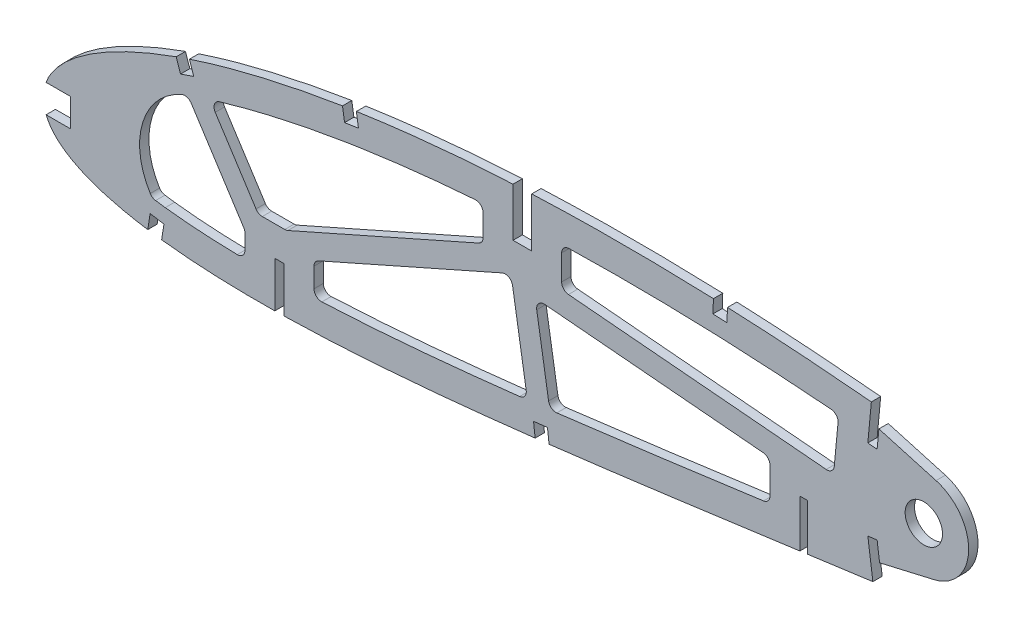
SolidWorks part; units mm, degrees
ref_plane "Front Plane" through (0, 0, 0) normal (0, 0, 1) x (1, 0, 0)
ref_plane "Top Plane" through (0, 0, 0) normal (0, 1, 0) x (1, 0, 0)
ref_plane "Right Plane" through (0, 0, 0) normal (1, 0, 0) x (0, 0, -1)
curve "Curve1"
  spline degree 3 poles (452.1031, 0.7048, 0) (452.0685, 0.7262, 0) (451.9301, 0.8117, 0) (451.6183, 1.003, 0) (451.099, 1.3216, 0) (450.372, 1.7653, 0) (449.438, 2.3329, 0) (448.2963, 3.0204, 0) (446.9478, 3.8257, 0) (445.3928, 4.7448, 0) (443.6314, 5.7736, 0) (441.6643, 6.9077, 0) (439.4916, 8.1409, 0) (437.1143, 9.468, 0) (434.5331, 10.8828, 0) (431.7485, 12.3789, 0) (428.7615, 13.9486, 0) (425.5733, 15.5853, 0) (422.1844, 17.2798, 0) (418.5964, 19.0251, 0) (414.8106, 20.8125, 0) (410.8282, 22.6325, 0) (406.6515, 24.4776, 0) (402.2816, 26.3365, 0) (397.7212, 28.201, 0) (392.972, 30.0605, 0) (388.0369, 31.9065, 0) (382.9178, 33.7272, 0) (377.6186, 35.5144, 0) (372.1418, 37.2567, 0) (366.4913, 38.9446, 0) (360.6704, 40.5671, 0) (354.684, 42.1159, 0) (348.5359, 43.5797, 0) (342.2312, 44.9487, 0) (335.775, 46.2147, 0) (329.1727, 47.3651, 0) (322.4425, 48.3989, 0) (315.6929, 49.2588, 0) (308.9571, 50.1023, 0) (302.2314, 50.8946, 0) (295.4235, 51.6533, 0) (288.5399, 52.3742, 0) (281.5875, 53.055, 0) (274.5733, 53.6928, 0) (267.5046, 54.2857, 0) (260.3883, 54.8303, 0) (253.2318, 55.3259, 0) (246.0422, 55.768, 0) (238.8272, 56.1563, 0) (231.5941, 56.4881, 0) (224.3504, 56.7611, 0) (217.1039, 56.9737, 0) (209.862, 57.1238, 0) (202.6326, 57.2105, 0) (195.4232, 57.2315, 0) (188.2416, 57.1863, 0) (181.0954, 57.0734, 0) (173.9924, 56.8912, 0) (166.9401, 56.6395, 0) (159.9462, 56.3182, 0) (153.0184, 55.9248, 0) (146.164, 55.4618, 0) (139.3909, 54.9271, 0) (132.7063, 54.3206, 0) (126.1174, 53.645, 0) (119.6314, 52.8983, 0) (113.2554, 52.0826, 0) (106.9962, 51.1996, 0) (100.8609, 50.2488, 0) (94.8561, 49.2329, 0) (88.9882, 48.153, 0) (83.2635, 47.0122, 0) (77.6882, 45.8109, 0) (72.2682, 44.5525, 0) (67.0092, 43.2395, 0) (61.9167, 41.874, 0) (56.9959, 40.4594, 0) (52.2519, 38.999, 0) (47.6902, 37.4943, 0) (43.3141, 35.951, 0) (39.1291, 34.3702, 0) (35.1384, 32.7568, 0) (31.3466, 31.113, 0) (27.7567, 29.4439, 0) (24.3726, 27.7512, 0) (21.1967, 26.0397, 0) (18.2324, 24.3122, 0) (15.4823, 22.5717, 0) (12.9477, 20.8227, 0) (10.632, 19.0664, 0) (8.5361, 17.307, 0) (6.6613, 15.5474, 0) (5.0102, 13.7886, 0) (3.5829, 12.0339, 0) (2.3811, 10.2847, 0) (1.4051, 8.5424, 0) (0.6571, 6.8085, 0) (0.1363, 5.084, 0) (-0.1488, 3.3712, 0) (-0.2197, 1.669, 0) (-0.0731, 0.5555, 0) (0, 0, 0) knots 0 0 0 0 0.000254 0.001015 0.002283 0.004057 0.006331 0.009105 0.012374 0.016134 0.02038 0.025106 0.030306 0.035972 0.0421 0.048678 0.055702 0.06316 0.071046 0.07935 0.088063 0.097176 0.106678 0.116562 0.126814 0.137428 0.148394 0.1597 0.171338 0.183298 0.19557 0.208144 0.221012 0.234162 0.247587 0.261277 0.275223 0.289414 0.303771 0.317689 0.331784 0.34604 0.360444 0.374983 0.38964 0.404403 0.419257 0.434187 0.449177 0.464215 0.479284 0.49437 0.509458 0.524532 0.539579 0.554583 0.56953 0.584403 0.599191 0.613877 0.628447 0.642889 0.657186 0.671326 0.685294 0.699078 0.712665 0.726043 0.739198 0.752118 0.764792 0.777208 0.789356 0.801224 0.812804 0.824083 0.835055 0.84571 0.856038 0.866034 0.875689 0.884998 0.893953 0.902553 0.910789 0.918661 0.926166 0.933303 0.940071 0.946475 0.952518 0.958205 0.963547 0.968557 0.97325 0.977651 0.981787 0.985694 0.989415 0.993001 0.996508 1 1 1 1
curve "Curve2"
  spline degree 3 poles (0, 0, 0) (0.1161, -0.5481, 0) (0.3488, -1.6467, 0) (0.9811, -3.2283, 0) (1.8173, -4.7487, 0) (2.8749, -6.2038, 0) (4.147, -7.5932, 0) (5.6306, -8.9184, 0) (7.3243, -10.1787, 0) (9.226, -11.3735, 0) (11.3328, -12.5041, 0) (13.6425, -13.5697, 0) (16.1528, -14.5701, 0) (18.8611, -15.5039, 0) (21.764, -16.3724, 0) (24.8588, -17.1737, 0) (28.1419, -17.9088, 0) (31.6103, -18.5759, 0) (35.26, -19.1755, 0) (39.0874, -19.7075, 0) (43.0885, -20.172, 0) (47.2594, -20.5682, 0) (51.596, -20.8969, 0) (56.0938, -21.1583, 0) (60.7487, -21.3533, 0) (65.556, -21.481, 0) (70.5112, -21.5436, 0) (75.6096, -21.5419, 0) (80.8464, -21.4754, 0) (86.2171, -21.3479, 0) (91.7164, -21.1586, 0) (97.3395, -20.9096, 0) (103.0813, -20.6036, 0) (108.9365, -20.2416, 0) (114.9002, -19.8251, 0) (120.967, -19.3576, 0) (127.1315, -18.8401, 0) (133.3883, -18.2757, 0) (139.7319, -17.6673, 0) (146.1567, -17.0167, 0) (152.6572, -16.327, 0) (159.2275, -15.6004, 0) (165.862, -14.8409, 0) (172.5546, -14.0497, 0) (179.2998, -13.2315, 0) (186.0911, -12.3877, 0) (192.923, -11.5217, 0) (199.7891, -10.6375, 0) (206.6832, -9.7349, 0) (213.5994, -8.8205, 0) (220.5311, -7.8935, 0) (227.4721, -6.9586, 0) (234.4161, -6.0188, 0) (241.3564, -5.0743, 0) (248.2868, -4.1291, 0) (255.2009, -3.1857, 0) (262.0918, -2.2442, 0) (268.9535, -1.3094, 0) (275.779, -0.3811, 0) (282.5619, 0.5389, 0) (289.2958, 1.4477, 0) (295.9744, 2.3443, 0) (302.5907, 3.228, 0) (309.138, 4.0992, 0) (315.5119, 4.9314, 0) (321.6955, 5.769, 0) (327.7099, 6.4556, 0) (333.6493, 7.0417, 0) (339.52, 7.5222, 0) (345.315, 7.9041, 0) (351.0275, 8.19, 0) (356.6509, 8.3839, 0) (362.1779, 8.4917, 0) (367.6017, 8.516, 0) (372.9148, 8.4647, 0) (378.1105, 8.3417, 0) (383.1813, 8.1528, 0) (388.1203, 7.9042, 0) (392.9205, 7.6027, 0) (397.5745, 7.2527, 0) (402.076, 6.8625, 0) (406.4179, 6.4377, 0) (410.5937, 5.9833, 0) (414.5972, 5.5086, 0) (418.4221, 5.0169, 0) (422.0625, 4.5163, 0) (425.5126, 4.0117, 0) (428.7669, 3.5097, 0) (431.8204, 3.015, 0) (434.6681, 2.5342, 0) (437.3055, 2.0718, 0) (439.7281, 1.6323, 0) (441.9324, 1.2212, 0) (443.9143, 0.8406, 0) (445.6709, 0.4968, 0) (447.199, 0.1913, 0) (448.4964, -0.0716, 0) (449.5609, -0.2909, 0) (450.3908, -0.463, 0) (450.9844, -0.5881, 0) (451.3411, -0.6626, 0) (451.4997, -0.6964, 0) (451.5393, -0.7048, 0) knots 0 0 0 0 0.003638 0.007293 0.011028 0.014901 0.018963 0.023258 0.027821 0.032679 0.037853 0.043362 0.049215 0.055422 0.061989 0.068918 0.076211 0.083868 0.091887 0.100266 0.109 0.118085 0.127515 0.137285 0.147388 0.157816 0.168563 0.179619 0.190977 0.202627 0.21456 0.226767 0.239236 0.251959 0.264924 0.27812 0.291536 0.30516 0.318981 0.332985 0.347163 0.361499 0.375981 0.390597 0.405333 0.420175 0.43511 0.450124 0.465203 0.480333 0.495501 0.51069 0.525887 0.541078 0.556247 0.571382 0.586466 0.601485 0.616424 0.631269 0.646007 0.660621 0.675098 0.689423 0.703582 0.716908 0.730009 0.742952 0.755726 0.76832 0.780724 0.792927 0.804916 0.816679 0.828204 0.839475 0.850481 0.861208 0.871639 0.881763 0.891564 0.901027 0.910139 0.918884 0.927249 0.935221 0.942785 0.949928 0.956638 0.962904 0.968712 0.974054 0.978918 0.983297 0.98718 0.990561 0.993433 0.995791 0.99763 0.998946 0.999737 1 1 1 1
sketch "Sketch1" plane through (0, 0, 0) normal (0, 0, 1) x (1, 0, 0)
  line L24 (452.1031, 0.7048) -> (456.094, -1.6764)
  line L25 (451.5393, -0.7048) -> (456.094, -1.6764)
  spline S2 degree 3 poles (-2902.3793, -755.52) (63.6454, 63.6466) (-7.9338, 19.0709) (0.9811, -3.2283) (1.8173, -4.7487) (2.8749, -6.2038) (4.147, -7.5932) (5.6306, -8.9184) (7.3243, -10.1787) (9.226, -11.3735) (11.3328, -12.5041) (13.6425, -13.5697) (16.1528, -14.5701) (18.8611, -15.5039) (21.764, -16.3724) (24.8588, -17.1737) (28.1419, -17.9088) (31.6103, -18.5759) (35.26, -19.1755) (39.0874, -19.7075) (43.0885, -20.172) (47.2594, -20.5682) (51.596, -20.8969) (56.0938, -21.1583) (60.7487, -21.3533) (65.556, -21.481) (70.5112, -21.5436) (75.6096, -21.5419) (80.8464, -21.4754) (86.2171, -21.3479) (91.7164, -21.1586) (97.3395, -20.9096) (103.0813, -20.6036) (108.9365, -20.2416) (114.9002, -19.8251) (120.967, -19.3576) (127.1315, -18.8401) (133.3883, -18.2757) (139.7319, -17.6673) (146.1567, -17.0167) (152.6572, -16.327) (159.2275, -15.6004) (165.862, -14.8409) (172.5546, -14.0497) (179.2998, -13.2315) (186.0911, -12.3877) (192.923, -11.5217) (199.7891, -10.6375) (206.6832, -9.7349) (213.5994, -8.8205) (220.5311, -7.8935) (227.4721, -6.9586) (234.4161, -6.0188) (241.3564, -5.0743) (248.2868, -4.1291) (255.2009, -3.1857) (262.0918, -2.2442) (268.9535, -1.3094) (275.779, -0.3811) (282.5619, 0.5389) (289.2958, 1.4477) (295.9744, 2.3443) (302.5907, 3.228) (309.138, 4.0992) (315.5119, 4.9314) (321.6955, 5.769) (327.7099, 6.4556) (333.6493, 7.0417) (339.52, 7.5222) (345.315, 7.9041) (351.0275, 8.19) (356.6509, 8.3839) (362.1779, 8.4917) (367.6017, 8.516) (372.9148, 8.4647) (378.1105, 8.3417) (383.1813, 8.1528) (388.1203, 7.9042) (392.9205, 7.6027) (397.5745, 7.2527) (402.076, 6.8625) (406.4179, 6.4377) (410.5937, 5.9833) (414.5972, 5.5086) (418.4221, 5.0169) (422.0625, 4.5163) (425.5126, 4.0117) (428.7669, 3.5097) (431.8204, 3.015) (434.6681, 2.5342) (437.3055, 2.0718) (439.7281, 1.6323) (441.9324, 1.2212) (443.9143, 0.8406) (445.6709, 0.4968) (447.199, 0.1913) (448.4964, -0.0716) (449.5609, -0.2909) (450.3908, -0.463) (450.9844, -0.5881) (467.4773, -4.0305) (482.2176, -14.7818) (1120.3699, 2922.8002) knots -0.14446 -0.14446 -0.14446 -0.14446 0.003638 0.007293 0.011028 0.014901 0.018963 0.023258 0.027821 0.032679 0.037853 0.043362 0.049215 0.055422 0.061989 0.068918 0.076211 0.083868 0.091887 0.100266 0.109 0.118085 0.127515 0.137285 0.147388 0.157816 0.168563 0.179619 0.190977 0.202627 0.21456 0.226767 0.239236 0.251959 0.264924 0.27812 0.291536 0.30516 0.318981 0.332985 0.347163 0.361499 0.375981 0.390597 0.405333 0.420175 0.43511 0.450124 0.465203 0.480333 0.495501 0.51069 0.525887 0.541078 0.556247 0.571382 0.586466 0.601485 0.616424 0.631269 0.646007 0.660621 0.675098 0.689423 0.703582 0.716908 0.730009 0.742952 0.755726 0.76832 0.780724 0.792927 0.804916 0.816679 0.828204 0.839475 0.850481 0.861208 0.871639 0.881763 0.891564 0.901027 0.910139 0.918884 0.927249 0.935221 0.942785 0.949928 0.956638 0.962904 0.968712 0.974054 0.978918 0.983297 0.98718 0.990561 0.993433 0.995791 0.99763 0.998946 0.999737 1.107215 1.107215 1.107215 1.107215 only from (0, 0) to (451.5393, -0.7048) construction
  spline S3 degree 3 poles (2072.0463, 2524.7843) (479.969, -24.2918) (467.6474, -8.829) (451.6183, 1.003) (451.099, 1.3216) (450.372, 1.7653) (449.438, 2.3329) (448.2963, 3.0204) (446.9478, 3.8257) (445.3928, 4.7448) (443.6314, 5.7736) (441.6643, 6.9077) (439.4916, 8.1409) (437.1143, 9.468) (434.5331, 10.8828) (431.7485, 12.3789) (428.7615, 13.9486) (425.5733, 15.5853) (422.1844, 17.2798) (418.5964, 19.0251) (414.8106, 20.8125) (410.8282, 22.6325) (406.6515, 24.4776) (402.2816, 26.3365) (397.7212, 28.201) (392.972, 30.0605) (388.0369, 31.9065) (382.9178, 33.7272) (377.6186, 35.5144) (372.1418, 37.2567) (366.4913, 38.9446) (360.6704, 40.5671) (354.684, 42.1159) (348.5359, 43.5797) (342.2312, 44.9487) (335.775, 46.2147) (329.1727, 47.3651) (322.4425, 48.3989) (315.6929, 49.2588) (308.9571, 50.1023) (302.2314, 50.8946) (295.4235, 51.6533) (288.5399, 52.3742) (281.5875, 53.055) (274.5733, 53.6928) (267.5046, 54.2857) (260.3883, 54.8303) (253.2318, 55.3259) (246.0422, 55.768) (238.8272, 56.1563) (231.5941, 56.4881) (224.3504, 56.7611) (217.1039, 56.9737) (209.862, 57.1238) (202.6326, 57.2105) (195.4232, 57.2315) (188.2416, 57.1863) (181.0954, 57.0734) (173.9924, 56.8912) (166.9401, 56.6395) (159.9462, 56.3182) (153.0184, 55.9248) (146.164, 55.4618) (139.3909, 54.9271) (132.7063, 54.3206) (126.1174, 53.645) (119.6314, 52.8983) (113.2554, 52.0826) (106.9962, 51.1996) (100.8609, 50.2488) (94.8561, 49.2329) (88.9882, 48.153) (83.2635, 47.0122) (77.6882, 45.8109) (72.2682, 44.5525) (67.0092, 43.2395) (61.9167, 41.874) (56.9959, 40.4594) (52.2519, 38.999) (47.6902, 37.4943) (43.3141, 35.951) (39.1291, 34.3702) (35.1384, 32.7568) (31.3466, 31.113) (27.7567, 29.4439) (24.3726, 27.7512) (21.1967, 26.0397) (18.2324, 24.3122) (15.4823, 22.5717) (12.9477, 20.8227) (10.632, 19.0664) (8.5361, 17.307) (6.6613, 15.5474) (5.0102, 13.7886) (3.5829, 12.0339) (2.3811, 10.2847) (1.4051, 8.5424) (0.6571, 6.8085) (0.1363, 5.084) (-0.1488, 3.3712) (-1.1473, -20.5831) (81.3582, -38.7525) (-2988.6181, -253.0424) knots -0.115084 -0.115084 -0.115084 -0.115084 0.000254 0.001015 0.002283 0.004057 0.006331 0.009105 0.012374 0.016134 0.02038 0.025106 0.030306 0.035972 0.0421 0.048678 0.055702 0.06316 0.071046 0.07935 0.088063 0.097176 0.106678 0.116562 0.126814 0.137428 0.148394 0.1597 0.171338 0.183298 0.19557 0.208144 0.221012 0.234162 0.247587 0.261277 0.275223 0.289414 0.303771 0.317689 0.331784 0.34604 0.360444 0.374983 0.38964 0.404403 0.419257 0.434187 0.449177 0.464215 0.479284 0.49437 0.509458 0.524532 0.539579 0.554583 0.56953 0.584403 0.599191 0.613877 0.628447 0.642889 0.657186 0.671326 0.685294 0.699078 0.712665 0.726043 0.739198 0.752118 0.764792 0.777208 0.789356 0.801224 0.812804 0.824083 0.835055 0.84571 0.856038 0.866034 0.875689 0.884998 0.893953 0.902553 0.910789 0.918661 0.926166 0.933303 0.940071 0.946475 0.952518 0.958205 0.963547 0.968557 0.97325 0.977651 0.981787 0.985694 0.989415 0.993001 0.996508 1.138367 1.138367 1.138367 1.138367 only from (452.1031, 0.7048) to (0, 0) construction
  spline S4 degree 3 poles (0, 0) (0.1161, -0.5481) (0.3488, -1.6467) (0.9811, -3.2283) (1.8173, -4.7487) (2.8749, -6.2038) (4.147, -7.5932) (5.6306, -8.9184) (7.3243, -10.1787) (9.226, -11.3735) (11.3328, -12.5041) (13.6425, -13.5697) (16.1528, -14.5701) (18.8611, -15.5039) (21.764, -16.3724) (24.8588, -17.1737) (28.1419, -17.9088) (31.6103, -18.5759) (35.26, -19.1755) (39.0874, -19.7075) (43.0885, -20.172) (47.2594, -20.5682) (51.596, -20.8969) (56.0938, -21.1583) (60.7487, -21.3533) (65.556, -21.481) (70.5112, -21.5436) (75.6096, -21.5419) (80.8464, -21.4754) (86.2171, -21.3479) (91.7164, -21.1586) (97.3395, -20.9096) (103.0813, -20.6036) (108.9365, -20.2416) (114.9002, -19.8251) (120.967, -19.3576) (127.1315, -18.8401) (133.3883, -18.2757) (139.7319, -17.6673) (146.1567, -17.0167) (152.6572, -16.327) (159.2275, -15.6004) (165.862, -14.8409) (172.5546, -14.0497) (179.2998, -13.2315) (186.0911, -12.3877) (192.923, -11.5217) (199.7891, -10.6375) (206.6832, -9.7349) (213.5994, -8.8205) (220.5311, -7.8935) (227.4721, -6.9586) (234.4161, -6.0188) (241.3564, -5.0743) (248.2868, -4.1291) (255.2009, -3.1857) (262.0918, -2.2442) (268.9535, -1.3094) (275.779, -0.3811) (282.5619, 0.5389) (289.2958, 1.4477) (295.9744, 2.3443) (302.5907, 3.228) (309.138, 4.0992) (315.5119, 4.9314) (321.6955, 5.769) (327.7099, 6.4556) (333.6493, 7.0417) (339.52, 7.5222) (345.315, 7.9041) (351.0275, 8.19) (356.6509, 8.3839) (362.1779, 8.4917) (367.6017, 8.516) (372.9148, 8.4647) (378.1105, 8.3417) (383.1813, 8.1528) (388.1203, 7.9042) (392.9205, 7.6027) (397.5745, 7.2527) (402.076, 6.8625) (406.4179, 6.4377) (410.5937, 5.9833) (414.5972, 5.5086) (418.4221, 5.0169) (422.0625, 4.5163) (425.5126, 4.0117) (428.7669, 3.5097) (431.8204, 3.015) (434.6681, 2.5342) (437.3055, 2.0718) (439.7281, 1.6323) (441.9324, 1.2212) (443.9143, 0.8406) (445.6709, 0.4968) (447.199, 0.1913) (448.4964, -0.0716) (449.5609, -0.2909) (450.3908, -0.463) (450.9844, -0.5881) (451.3411, -0.6626) (451.4997, -0.6964) (451.5393, -0.7048) knots 0 0 0 0 0.003638 0.007293 0.011028 0.014901 0.018963 0.023258 0.027821 0.032679 0.037853 0.043362 0.049215 0.055422 0.061989 0.068918 0.076211 0.083868 0.091887 0.100266 0.109 0.118085 0.127515 0.137285 0.147388 0.157816 0.168563 0.179619 0.190977 0.202627 0.21456 0.226767 0.239236 0.251959 0.264924 0.27812 0.291536 0.30516 0.318981 0.332985 0.347163 0.361499 0.375981 0.390597 0.405333 0.420175 0.43511 0.450124 0.465203 0.480333 0.495501 0.51069 0.525887 0.541078 0.556247 0.571382 0.586466 0.601485 0.616424 0.631269 0.646007 0.660621 0.675098 0.689423 0.703582 0.716908 0.730009 0.742952 0.755726 0.76832 0.780724 0.792927 0.804916 0.816679 0.828204 0.839475 0.850481 0.861208 0.871639 0.881763 0.891564 0.901027 0.910139 0.918884 0.927249 0.935221 0.942785 0.949928 0.956638 0.962904 0.968712 0.974054 0.978918 0.983297 0.98718 0.990561 0.993433 0.995791 0.99763 0.998946 0.999737 1 1 1 1
  spline S5 degree 3 poles (452.1031, 0.7048) (452.0685, 0.7262) (451.9301, 0.8117) (451.6183, 1.003) (451.099, 1.3216) (450.372, 1.7653) (449.438, 2.3329) (448.2963, 3.0204) (446.9478, 3.8257) (445.3928, 4.7448) (443.6314, 5.7736) (441.6643, 6.9077) (439.4916, 8.1409) (437.1143, 9.468) (434.5331, 10.8828) (431.7485, 12.3789) (428.7615, 13.9486) (425.5733, 15.5853) (422.1844, 17.2798) (418.5964, 19.0251) (414.8106, 20.8125) (410.8282, 22.6325) (406.6515, 24.4776) (402.2816, 26.3365) (397.7212, 28.201) (392.972, 30.0605) (388.0369, 31.9065) (382.9178, 33.7272) (377.6186, 35.5144) (372.1418, 37.2567) (366.4913, 38.9446) (360.6704, 40.5671) (354.684, 42.1159) (348.5359, 43.5797) (342.2312, 44.9487) (335.775, 46.2147) (329.1727, 47.3651) (322.4425, 48.3989) (315.6929, 49.2588) (308.9571, 50.1023) (302.2314, 50.8946) (295.4235, 51.6533) (288.5399, 52.3742) (281.5875, 53.055) (274.5733, 53.6928) (267.5046, 54.2857) (260.3883, 54.8303) (253.2318, 55.3259) (246.0422, 55.768) (238.8272, 56.1563) (231.5941, 56.4881) (224.3504, 56.7611) (217.1039, 56.9737) (209.862, 57.1238) (202.6326, 57.2105) (195.4232, 57.2315) (188.2416, 57.1863) (181.0954, 57.0734) (173.9924, 56.8912) (166.9401, 56.6395) (159.9462, 56.3182) (153.0184, 55.9248) (146.164, 55.4618) (139.3909, 54.9271) (132.7063, 54.3206) (126.1174, 53.645) (119.6314, 52.8983) (113.2554, 52.0826) (106.9962, 51.1996) (100.8609, 50.2488) (94.8561, 49.2329) (88.9882, 48.153) (83.2635, 47.0122) (77.6882, 45.8109) (72.2682, 44.5525) (67.0092, 43.2395) (61.9167, 41.874) (56.9959, 40.4594) (52.2519, 38.999) (47.6902, 37.4943) (43.3141, 35.951) (39.1291, 34.3702) (35.1384, 32.7568) (31.3466, 31.113) (27.7567, 29.4439) (24.3726, 27.7512) (21.1967, 26.0397) (18.2324, 24.3122) (15.4823, 22.5717) (12.9477, 20.8227) (10.632, 19.0664) (8.5361, 17.307) (6.6613, 15.5474) (5.0102, 13.7886) (3.5829, 12.0339) (2.3811, 10.2847) (1.4051, 8.5424) (0.6571, 6.8085) (0.1363, 5.084) (-0.1488, 3.3712) (-0.2197, 1.669) (-0.0731, 0.5555) (0, 0) knots 0 0 0 0 0.000254 0.001015 0.002283 0.004057 0.006331 0.009105 0.012374 0.016134 0.02038 0.025106 0.030306 0.035972 0.0421 0.048678 0.055702 0.06316 0.071046 0.07935 0.088063 0.097176 0.106678 0.116562 0.126814 0.137428 0.148394 0.1597 0.171338 0.183298 0.19557 0.208144 0.221012 0.234162 0.247587 0.261277 0.275223 0.289414 0.303771 0.317689 0.331784 0.34604 0.360444 0.374983 0.38964 0.404403 0.419257 0.434187 0.449177 0.464215 0.479284 0.49437 0.509458 0.524532 0.539579 0.554583 0.56953 0.584403 0.599191 0.613877 0.628447 0.642889 0.657186 0.671326 0.685294 0.699078 0.712665 0.726043 0.739198 0.752118 0.764792 0.777208 0.789356 0.801224 0.812804 0.824083 0.835055 0.84571 0.856038 0.866034 0.875689 0.884998 0.893953 0.902553 0.910789 0.918661 0.926166 0.933303 0.940071 0.946475 0.952518 0.958205 0.963547 0.968557 0.97325 0.977651 0.981787 0.985694 0.989415 0.993001 0.996508 1 1 1 1
extrude "Boss-Extrude1" add sketch "Sketch1" along normal blind 3.175
sketch "Sketch2" plane through (0, 0, 0) normal (0, 0, -1) x (-1, 0, 0)
  line L0 (-81.6491, -6.0107) -> (-78.4741, -6.0107)
  line L1 (-81.6491, -20.9228) -> (-81.6491, -22.4869)
  line L2 (-259.4491, 13.2207) -> (-259.4491, -2.6526)
  line L4 (-81.6491, -22.4869) -> (-78.4741, -21.7048)
  line L5 (-78.4741, -21.7048) -> (-78.4741, -20.9228)
  line L7 (-165.7866, 56.5935) -> (-165.7866, 39.7629)
  line L8 (-165.7866, 39.7629) -> (-159.4366, 39.7629)
  line L9 (-165.7866, 56.5935) -> (-165.7866, 58.5208)
  line L10 (-81.6491, -6.0107) -> (-81.6491, -20.9228)
  line L12 (-165.7866, 58.5208) -> (-159.4366, 57.5572)
  line L13 (-159.4366, 57.5572) -> (-159.4366, 56.5935)
  line L14 (-78.4741, -6.0107) -> (-78.4741, -20.9228)
  line L16 (-259.4491, 13.2207) -> (-256.9091, 13.2207)
  line L17 (-259.4491, -2.6526) -> (-259.4491, -5.0698)
  line L19 (-159.4366, 56.5935) -> (-159.4366, 39.7629)
  line L20 (-259.4491, -5.0698) -> (-256.9091, -3.8612)
  line L21 (-256.9091, -3.8612) -> (-256.9091, -2.6526)
  line L22 (-256.9091, 13.2207) -> (-256.9091, -2.6526)
extrude "Cut-Extrude1" cut sketch "Sketch2" against normal blind 7.62
sketch "Sketch3" plane through (0, 0, 0) normal (0, 0, -1) x (-1, 0, 0)
  circle A1 centre (-299.0384, 26.2554) radius 6.35
extrude "Cut-Extrude2" cut sketch "Sketch3" against normal blind 7.62
sketch "Sketch4" plane through (0, 0, 3.175) normal (0, 0, 1) x (1, 0, 0)
  line L0 (283.1634, 40.1032) -> (284.3809, 52.7385)
  line L1 (283.1634, 40.1032) -> (284.3809, 52.7385)
  line L2 (284.8624, 0.8345) -> (283.1634, 13.4207)
  line L3 (284.8624, 0.8345) -> (283.1634, 13.4207)
  line L4 (283.1634, 13.4207) -> (280.017, 12.9956)
  line L5 (283.1634, 13.4207) -> (280.017, 12.9956)
  line L6 (280.003, 40.404) -> (283.1634, 40.1032)
  line L7 (280.003, 40.404) -> (283.1634, 40.1032)
  line L8 (280.017, 12.9956) -> (281.7174, 0.4099)
  line L9 (280.017, 12.9956) -> (281.7174, 0.4099)
  line L10 (281.2061, 53.046) -> (280.003, 40.404)
  line L11 (281.2061, 53.046) -> (280.003, 40.404)
  line L12 (227.543, 56.7883) -> (227.3611, 52.0373)
  line L13 (227.543, 56.7883) -> (227.3611, 52.0373)
  line L14 (101.4521, 50.4601) -> (102.1913, 45.7722)
  line L15 (101.4521, 50.4601) -> (102.1913, 45.7722)
  line L16 (44.909, 36.6556) -> (46.4387, 32.1792)
  line L17 (44.909, 36.6556) -> (46.4387, 32.1792)
  line L18 (166.4044, -10.0397) -> (166.9563, -14.7725)
  line L19 (166.4044, -10.0397) -> (166.9563, -14.7725)
  line L20 (36.1137, -14.0525) -> (35.373, -18.771)
  line L21 (36.1137, -14.0525) -> (35.373, -18.771)
  line L22 (40.8104, -14.7911) -> (36.1137, -14.0525)
  line L23 (40.8104, -14.7911) -> (36.1137, -14.0525)
  line L24 (171.134, -9.4806) -> (166.4044, -10.0397)
  line L25 (171.134, -9.4806) -> (166.4044, -10.0397)
  line L26 (50.9453, 33.7189) -> (49.4124, 38.2061)
  line L27 (50.9453, 33.7189) -> (49.4124, 38.2061)
  line L28 (40.0562, -19.5592) -> (40.8104, -14.7911)
  line L29 (40.0562, -19.5592) -> (40.8104, -14.7911)
  line L30 (106.9007, 46.4815) -> (106.1899, 51.2009)
  line L31 (106.9007, 46.4815) -> (106.1899, 51.2009)
  line L32 (232.1192, 51.8391) -> (232.3281, 56.5914)
  line L33 (232.1192, 51.8391) -> (232.3281, 56.5914)
  line L34 (171.6935, -14.2138) -> (171.134, -9.4806)
  line L35 (171.6935, -14.2138) -> (171.134, -9.4806)
  line L36 (227.3611, 52.0373) -> (232.1192, 51.8391)
  line L37 (227.3611, 52.0373) -> (232.1192, 51.8391)
  line L38 (102.1913, 45.7722) -> (106.9007, 46.4815)
  line L39 (102.1913, 45.7722) -> (106.9007, 46.4815)
  line L40 (-0.4483, -2.6341) -> (9.0767, -2.6341)
  line L41 (-0.4483, -2.6341) -> (9.0767, -2.6341)
  line L42 (-0.4483, 6.8909) -> (9.0767, 6.8909)
  line L43 (-0.4483, 6.8909) -> (9.0767, 6.8909)
  line L44 (9.0767, -2.6341) -> (9.0767, 6.8909)
  line L45 (9.0767, -2.6341) -> (9.0767, 6.8909)
  line L46 (46.4387, 32.1792) -> (50.9453, 33.7189)
  line L47 (46.4387, 32.1792) -> (50.9453, 33.7189)
  line L48 (281.7174, 0.4099) -> (282.0892, -2.3425)
  line L49 (282.0892, -2.3425) -> (285.2356, -1.9174)
  line L50 (285.2356, -1.9174) -> (284.8624, 0.8345)
  line L51 (281.2061, 53.046) -> (281.5903, 57.0828)
  line L52 (281.5903, 57.0828) -> (284.7703, 56.7802)
  line L53 (284.7703, 56.7802) -> (284.3809, 52.7385)
  line L54 (227.543, 56.7883) -> (232.3281, 56.5914)
  line L55 (101.4521, 50.4601) -> (106.1899, 51.2009)
  line L56 (44.909, 36.6556) -> (49.4124, 38.2061)
  line L57 (-0.4483, -2.6341) -> (-0.4483, 6.8909)
  line L58 (35.373, -18.771) -> (34.8729, -21.9571)
  line L59 (34.8729, -21.9571) -> (39.5676, -22.6941)
  line L60 (39.5676, -22.6941) -> (40.0562, -19.5592)
  line L61 (166.9563, -14.7725) -> (171.6935, -14.2138)
  line L62 (283.7722, 46.4209) -> (303.193, 40.9182)
  line L63 (284.0129, 7.1276) -> (302.4805, 11.4092)
  line L64 (284.3809, 52.7385) -> (466.0882, 52.7385)
  line L65 (466.0882, 52.7385) -> (466.0882, -18.771)
  line L66 (466.0882, -18.771) -> (284.8624, 0.8345)
  circle A0 centre (299.0384, 26.2554) radius 6.35 construction
  circle A1 centre (299.0384, 26.2554) radius 6.35
  circle A2 centre (299.0384, 26.2554) radius 15.24
  dimension "D1" = 30.48
extrude "Cut-Extrude3" cut sketch "Sketch4" against normal through all
sketch "Sketch5" plane through (0, 0, 3.175) normal (0, 0, 1) x (1, 0, 0)
  line L0 (36.8297, -9.1216) -> (41.2489, -9.7235)
  line L1 (48.3594, 26.9518) -> (52.6619, 28.4309)
  line L2 (103.0835, 40.3016) -> (107.7147, 41.0203)
  line L3 (227.1599, 46.4854) -> (231.8893, 46.2967)
  line L4 (165.7688, -4.6187) -> (170.4819, -4.0617)
  line L5 (169.5966, 39.7629) -> (169.5966, 56.2793)
  line L6 (68.3141, -21.5029) -> (68.3141, 4.1493)
  line L7 (68.3141, 4.1493) -> (91.8091, 4.1493)
  line L8 (91.8091, 4.1493) -> (91.8091, -21.4504)
  line L9 (175.9466, 56.5794) -> (175.9466, 29.6029)
  line L10 (175.9466, 29.6029) -> (149.2766, 29.6029)
  line L11 (149.2766, 29.6029) -> (149.2766, 56.2793)
  line L12 (246.7491, -2.9522) -> (246.7491, 23.3807)
  line L13 (246.7491, 23.3807) -> (269.6091, 23.3807)
  line L14 (269.6091, 23.3807) -> (269.6091, -2.6054)
  line L15 (268.177, 23.3807) -> (271.0953, 54.0451)
  line L16 (269.8887, 41.3666) -> (271.0953, 54.0451) construction
  line L17 (52.6619, 28.4309) -> (68.3141, 4.1493) construction
  line L18 (91.8091, 4.1493) -> (149.2766, 29.6029) construction
  line L19 (168.1254, -4.3402) -> (162.6116, 29.6029) construction
  line L20 (246.7491, 23.3807) -> (175.9466, 29.6029) construction
  line L21 (48.9512, 27.1553) -> (68.3141, -2.8828)
  line L22 (91.8091, -0.0177) -> (158.6846, 29.6029)
  line L23 (171.9123, -3.8905) -> (166.3723, 30.2138)
  line L24 (268.3602, 25.3062) -> (175.9466, 33.4276)
  line L25 (55.8642, 30.4952) -> (72.8471, 4.1493)
  line L26 (82.4011, 4.1493) -> (149.2766, 33.7699)
  line L27 (164.3647, -4.9511) -> (158.7516, 29.6029)
  line L28 (246.7491, 19.5561) -> (166.9646, 26.5675)
  line L29 (49.4595, 26.3667) -> (65.1117, 2.085) construction
  line L30 (55.8642, 30.4952) -> (71.5164, 6.2135) construction
  line L31 (90.2661, 7.6329) -> (147.7336, 33.0865) construction
  line L32 (93.352, 0.6657) -> (150.8195, 26.1193) construction
  line L33 (246.4155, 19.5854) -> (175.613, 25.8075) construction
  line L34 (247.0826, 27.1761) -> (176.2801, 33.3982) construction
  line L35 (164.3647, -4.9511) -> (158.8509, 28.992) construction
  line L36 (9.0767, 6.8909) -> (9.0767, -2.6341)
  line L37 (9.0767, -2.6341) -> (0.7554, -2.6341)
  line L38 (35.3108, -19.1674) -> (36.1137, -14.0525)
  line L39 (36.1137, -14.0525) -> (40.8104, -14.7911)
  line L40 (40.8104, -14.7911) -> (40.0562, -19.5592)
  line L41 (40.0562, -19.5592) -> (40.0174, -19.8086)
  line L42 (78.4741, -21.5029) -> (78.4741, -6.0107)
  line L43 (78.4741, -6.0107) -> (81.6491, -6.0107)
  line L44 (81.6491, -6.0107) -> (81.6491, -21.4504)
  line L45 (166.949, -14.7099) -> (166.4044, -10.0397)
  line L46 (166.4044, -10.0397) -> (171.134, -9.4806)
  line L47 (171.134, -9.4806) -> (171.686, -14.1501)
  line L48 (256.9091, -2.9522) -> (256.9091, 13.2207)
  line L49 (256.9091, 13.2207) -> (259.4491, 13.2207)
  line L50 (259.4491, 13.2207) -> (259.4491, -2.6054)
  line L51 (281.7155, 0.4236) -> (280.017, 12.9956)
  line L52 (280.017, 12.9956) -> (283.1634, 13.4207)
  line L53 (283.1634, 13.4207) -> (284.0129, 7.1276)
  line L54 (284.0129, 7.1276) -> (302.4805, 11.4092)
  line L55 (303.193, 40.9182) -> (283.7722, 46.4209)
  line L56 (283.7722, 46.4209) -> (283.1634, 40.1032)
  line L57 (283.1634, 40.1032) -> (280.003, 40.404)
  line L58 (280.003, 40.404) -> (281.2096, 53.0825)
  line L59 (232.3218, 56.4475) -> (232.1192, 51.8391)
  line L60 (232.1192, 51.8391) -> (227.3611, 52.0373)
  line L61 (227.3611, 52.0373) -> (227.5373, 56.6384)
  line L62 (165.7866, 56.5794) -> (165.7866, 39.7629)
  line L63 (165.7866, 39.7629) -> (159.4366, 39.7629)
  line L64 (159.4366, 39.7629) -> (159.4366, 56.2793)
  line L65 (106.2099, 51.0682) -> (106.9007, 46.4815)
  line L66 (106.9007, 46.4815) -> (102.1913, 45.7722)
  line L67 (102.1913, 45.7722) -> (101.4722, 50.3331)
  line L68 (49.458, 38.0725) -> (50.9453, 33.7189)
  line L69 (50.9453, 33.7189) -> (46.4387, 32.1792)
  line L70 (46.4387, 32.1792) -> (44.954, 36.5241)
  line L71 (0.7247, 6.8909) -> (9.0767, 6.8909)
  line L72 (9.0767, 6.8909) -> (9.0767, -2.6341)
  line L73 (9.0767, -2.6341) -> (0.7554, -2.6341)
  line L74 (35.3108, -19.1674) -> (36.1137, -14.0525)
  line L75 (36.1137, -14.0525) -> (40.8104, -14.7911)
  line L76 (40.8104, -14.7911) -> (40.0562, -19.5592)
  line L77 (40.0562, -19.5592) -> (40.0174, -19.8086)
  line L78 (78.4741, -21.5029) -> (78.4741, -6.0107)
  line L79 (78.4741, -6.0107) -> (81.6491, -6.0107)
  line L80 (81.6491, -6.0107) -> (81.6491, -21.4504)
  line L81 (166.949, -14.7099) -> (166.4044, -10.0397)
  line L82 (166.4044, -10.0397) -> (171.134, -9.4806)
  line L83 (171.134, -9.4806) -> (171.686, -14.1501)
  line L84 (256.9091, -2.9522) -> (256.9091, 13.2207)
  line L85 (256.9091, 13.2207) -> (259.4491, 13.2207)
  line L86 (259.4491, 13.2207) -> (259.4491, -2.6054)
  line L87 (281.7155, 0.4236) -> (280.017, 12.9956)
  line L88 (280.017, 12.9956) -> (283.1634, 13.4207)
  line L89 (283.1634, 13.4207) -> (284.0129, 7.1276)
  line L90 (284.0129, 7.1276) -> (302.4805, 11.4092)
  line L91 (303.193, 40.9182) -> (283.7722, 46.4209)
  line L92 (283.7722, 46.4209) -> (283.1634, 40.1032)
  line L93 (283.1634, 40.1032) -> (280.003, 40.404)
  line L94 (280.003, 40.404) -> (281.2096, 53.0825)
  line L95 (232.3218, 56.4475) -> (232.1192, 51.8391)
  line L96 (232.1192, 51.8391) -> (227.3611, 52.0373)
  line L97 (227.3611, 52.0373) -> (227.5373, 56.6384)
  line L98 (165.7866, 56.5794) -> (165.7866, 39.7629)
  line L99 (165.7866, 39.7629) -> (159.4366, 39.7629)
  line L100 (159.4366, 39.7629) -> (159.4366, 56.2793)
  line L101 (106.2099, 51.0682) -> (106.9007, 46.4815)
  line L102 (106.9007, 46.4815) -> (102.1913, 45.7722)
  line L103 (102.1913, 45.7722) -> (101.4722, 50.3331)
  line L104 (49.458, 38.0725) -> (50.9453, 33.7189)
  line L105 (50.9453, 33.7189) -> (46.4387, 32.1792)
  line L106 (46.4387, 32.1792) -> (44.954, 36.5241)
  line L107 (0.7247, 6.8909) -> (9.0767, 6.8909)
  line L108 (171.8861, -3.7293) -> (166.3723, 30.2138) construction
  arc A0 (48.3594, 26.9518) -> (36.8297, -9.1216) centre (56.3388, 4.5222) ccw
  arc A1 (302.4805, 11.4092) -> (303.193, 40.9182) centre (299.0384, 26.2554) ccw
  arc A2 (302.4805, 11.4092) -> (303.193, 40.9182) centre (299.0384, 26.2554) ccw
  arc A3 (155.7389, 28.2982) -> (159.2747, 26.3831) centre (156.7675, 25.9758) cw
  spline S0 degree 1 poles (48.3594, 26.9518) (10.2443, 3.3408) knots 0 0 1 1 construction
  spline S1 degree 3 poles (48.3594, 26.9518) (46.3271, 26.2288) (42.2727, 24.7134) (36.3512, 22.2504) (30.6067, 19.5659) (25.1156, 16.6373) (19.9897, 13.4418) (16.1914, 10.5527) (13.6295, 8.1613) (12.2956, 6.6705) (11.4374, 5.5303) (10.9076, 4.7161) (10.5723, 4.0993) (10.3642, 3.6463) (10.2835, 3.4459) (10.2443, 3.3408) knots 0.87196 0.87196 0.87196 0.87196 0.886143 0.900325 0.914508 0.928691 0.942874 0.957057 0.964148 0.97124 0.974785 0.978331 0.981877 0.98365 0.985422 0.985422 0.985422 0.985422
  spline S2 degree 1 poles (103.0835, 40.3016) (52.6619, 28.4309) knots 0 0 1 1 construction
  spline S3 degree 3 poles (103.0835, 40.3016) (98.7884, 39.6117) (90.2072, 38.101) (77.4851, 35.416) (64.9143, 32.2473) (56.7277, 29.782) (52.6619, 28.4309) knots 0.750752 0.750752 0.750752 0.750752 0.778577 0.806402 0.834226 0.862051 0.862051 0.862051 0.862051
  spline S4 degree 1 poles (159.9656, 46.133) (107.7147, 41.0203) knots 0 0 1 1 construction
  spline S5 degree 3 poles (159.9656, 46.133) (155.5848, 45.9046) (146.8227, 45.3584) (133.729, 44.2514) (120.6796, 42.8345) (112.0321, 41.6668) (107.7147, 41.0203) knots 0.629467 0.629467 0.629467 0.629467 0.657295 0.685123 0.71295 0.740778 0.740778 0.740778 0.740778
  spline S6 degree 1 poles (227.1599, 46.4854) (166.218, 46.4286) knots 0 0 1 1 construction
  spline S7 degree 3 poles (227.1599, 46.4854) (222.0775, 46.6743) (211.9065, 46.9628) (196.6607, 47.1116) (181.4242, 46.9602) (171.2863, 46.644) (166.218, 46.4286) knots 0.487735 0.487735 0.487735 0.487735 0.519862 0.551988 0.584115 0.616241 0.616241 0.616241 0.616241
  spline S8 degree 1 poles (280.2583, 42.9671) (231.8893, 46.2967) knots 0 0 1 1 construction
  spline S9 degree 3 poles (280.2583, 42.9671) (276.2333, 43.3456) (268.1781, 44.0543) (256.0871, 44.9675) (243.9908, 45.7255) (235.9242, 46.1248) (231.8893, 46.2967) knots 0.375811 0.375811 0.375811 0.375811 0.401301 0.426792 0.452283 0.477773 0.477773 0.477773 0.477773
  spline S10 degree 3 poles (3992.8623, -198.0274) (86.5026, 116.4928) (-15.3884, 26.5352) (1.8173, -4.7487) (2.8749, -6.2038) (4.147, -7.5932) (5.6306, -8.9184) (7.3243, -10.1787) (9.226, -11.3735) (11.3328, -12.5041) (13.6425, -13.5697) (16.1528, -14.5701) (18.8611, -15.5039) (21.764, -16.3724) (24.8588, -17.1737) (28.1419, -17.9088) (31.6103, -18.5759) (201.7481, -46.5295) (413.6536, 210.2942) (-811.1634, -3905.4854) knots -0.216848 -0.216848 -0.216848 -0.216848 0.007293 0.011028 0.014901 0.018963 0.023258 0.027821 0.032679 0.037853 0.043362 0.049215 0.055422 0.061989 0.068918 0.076211 0.083868 0.091887 1.197548 1.197548 1.197548 1.197548 only from (0.7554, -2.6341) to (35.3108, -19.1674)
  spline S11 degree 3 poles (610.5425, 3912.7347) (-269.6469, 230.7631) (-123.4126, -4.3556) (47.2594, -20.5682) (51.596, -20.8969) (56.0938, -21.1583) (60.7487, -21.3533) (65.556, -21.481) (70.5112, -21.5436) (333.9539, -21.4548) (594.0601, 224.2468) (515.8516, -3934.1604) knots -0.987507 -0.987507 -0.987507 -0.987507 0.109 0.118085 0.127515 0.137285 0.147388 0.157816 0.168563 0.179619 1.871275 1.871275 1.871275 1.871275 only from (40.0174, -19.8086) to (78.4741, -21.5029)
  spline S12 degree 3 poles (-392.9493, 3866.1073) (-548.7966, 249.7731) (-225.1999, -32.0714) (91.7164, -21.1586) (97.3395, -20.9096) (103.0813, -20.6036) (108.9365, -20.2416) (114.9002, -19.8251) (120.967, -19.3576) (127.1315, -18.8401) (133.3883, -18.2757) (139.7319, -17.6673) (146.1567, -17.0167) (152.6572, -16.327) (159.2275, -15.6004) (558.586, 30.1193) (940.5558, 206.0827) (1712.8739, -3544.3584) knots -1.83573 -1.83573 -1.83573 -1.83573 0.202627 0.21456 0.226767 0.239236 0.251959 0.264924 0.27812 0.291536 0.30516 0.318981 0.332985 0.347163 0.361499 0.375981 2.961662 2.961662 2.961662 2.961662 only from (81.6491, -21.4504) to (166.949, -14.7099)
  spline S13 degree 3 poles (-1326.663, 3568.4175) (-585.5989, -8.5131) (-198.5196, -59.0633) (179.2998, -13.2315) (186.0911, -12.3877) (192.923, -11.5217) (199.7891, -10.6375) (206.6832, -9.7349) (213.5994, -8.8205) (220.5311, -7.8935) (227.4721, -6.9586) (234.4161, -6.0188) (241.3564, -5.0743) (248.2868, -4.1291) (665.2531, 52.7636) (1079.0271, 115.7989) (1985.1056, -3445.8201) knots -2.055279 -2.055279 -2.055279 -2.055279 0.390597 0.405333 0.420175 0.43511 0.450124 0.465203 0.480333 0.495501 0.51069 0.525887 0.541078 0.556247 0.571382 3.278272 3.278272 3.278272 3.278272 only from (171.686, -14.1501) to (256.9091, -2.9522)
  spline S14 degree 3 poles (-1470.052, 3438.923) (-562.3107, -128.8763) (-148.7755, -58.2208) (268.9535, -1.3094) (771.9383, 67.1019) (1275.4625, 114.4081) (2235.9513, -3256.9103) knots -2.125701 -2.125701 -2.125701 -2.125701 0.586466 0.601485 0.616424 3.888141 3.888141 3.888141 3.888141 only from (259.4491, -2.6054) to (281.7155, 0.4236)
  spline S15 degree 3 poles (-560.5184, -2824.4058) (1981.2507, -1330.9347) (1179.4655, -22.2057) (267.5046, 54.2857) (260.3883, 54.8303) (253.2318, 55.3259) (246.0422, 55.768) (-259.5921, 82.9803) (-783.6499, -306.7056) (-734.2643, -3616.5485) knots -5.2927 -5.2927 -5.2927 -5.2927 0.38964 0.404403 0.419257 0.434187 0.449177 0.464215 3.594647 3.594647 3.594647 3.594647 only from (281.2096, 53.0825) to (232.3218, 56.4475)
  spline S16 degree 3 poles (93.2558, 3549.9709) (1710.4415, -991.1608) (981.8336, 34.5382) (217.1039, 56.9737) (209.862, 57.1238) (202.6326, 57.2105) (195.4232, 57.2315) (188.2416, 57.1863) (181.0954, 57.0734) (173.9924, 56.8912) (-190.7158, 43.8718) (-541.4237, -255.3112) (-261.6004, -3810.7074) knots -4.250537 -4.250537 -4.250537 -4.250537 0.49437 0.509458 0.524532 0.539579 0.554583 0.56953 0.584403 0.599191 0.613877 2.862147 2.862147 2.862147 2.862147 only from (227.5373, 56.6384) to (165.7866, 56.5794)
  spline S17 degree 3 poles (-1035.6907, -3044.1729) (1577.1681, -935.2487) (829.1628, 101.6043) (146.164, 55.4618) (139.3909, 54.9271) (132.7063, 54.3206) (126.1174, 53.645) (119.6314, 52.8983) (113.2554, 52.0826) (-245.6004, 1.4583) (-540.5092, -466.9711) (628.9059, -3793.1404) knots -3.601254 -3.601254 -3.601254 -3.601254 0.642889 0.657186 0.671326 0.685294 0.699078 0.712665 0.726043 0.739198 2.97458 2.97458 2.97458 2.97458 only from (159.4366, 56.2793) to (106.2099, 51.0682)
  spline S18 degree 3 poles (-1346.8212, 3648.3869) (1152.5481, -540.6084) (564.0987, 128.6186) (94.8561, 49.2329) (88.9882, 48.153) (83.2635, 47.0122) (77.6882, 45.8109) (72.2682, 44.5525) (67.0092, 43.2395) (61.9167, 41.874) (56.9959, 40.4594) (-171.6786, -29.9378) (-293.6539, -429.6473) (1586.4769, -3594.6122) knots -2.193096 -2.193096 -2.193096 -2.193096 0.752118 0.764792 0.777208 0.789356 0.801224 0.812804 0.824083 0.835055 0.84571 0.856038 2.328338 2.328338 2.328338 2.328338 only from (101.4722, 50.3331) to (49.458, 38.0725)
  spline S19 degree 3 poles (-1523.7253, 3677.395) (557.6605, -128.9227) (241.5098, 110.8144) (39.1291, 34.3702) (35.1384, 32.7568) (31.3466, 31.113) (27.7567, 29.4439) (24.3726, 27.7512) (21.1967, 26.0397) (18.2324, 24.3122) (15.4823, 22.5717) (12.9477, 20.8227) (10.632, 19.0664) (8.5361, 17.307) (6.6613, 15.5474) (5.0102, 13.7886) (3.5829, 12.0339) (2.3811, 10.2847) (-23.6357, -36.1565) (148.4291, -180.3819) (3984.9723, 269.5811) knots -0.456202 -0.456202 -0.456202 -0.456202 0.875689 0.884998 0.893953 0.902553 0.910789 0.918661 0.926166 0.933303 0.940071 0.946475 0.952518 0.958205 0.963547 0.968557 0.97325 0.977651 0.981787 1.304969 1.304969 1.304969 1.304969 only from (44.954, 36.5241) to (0.7247, 6.8909)
  spline S20 degree 3 poles (0.7554, -2.6341) (0.8346, -2.8252) (1.1527, -3.5402) (1.8173, -4.7487) (2.8749, -6.2038) (4.147, -7.5932) (5.6306, -8.9184) (7.3243, -10.1787) (9.226, -11.3735) (11.3328, -12.5041) (13.6425, -13.5697) (16.1528, -14.5701) (18.8611, -15.5039) (21.764, -16.3724) (24.8588, -17.1737) (28.1419, -17.9088) (31.6103, -18.5759) (34.0231, -18.9723) (35.2764, -19.1622) (35.3108, -19.1674) knots 0.005949 0.005949 0.005949 0.005949 0.007293 0.011028 0.014901 0.018963 0.023258 0.027821 0.032679 0.037853 0.043362 0.049215 0.055422 0.061989 0.068918 0.076211 0.083868 0.091887 0.092113 0.092113 0.092113 0.092113
  spline S21 degree 3 poles (40.0174, -19.8086) (41.0228, -19.9313) (43.4171, -20.2032) (47.2594, -20.5682) (51.596, -20.8969) (56.0938, -21.1583) (60.7487, -21.3533) (65.556, -21.481) (70.5112, -21.5436) (74.8337, -21.5421) (77.5038, -21.5157) (78.4741, -21.5029) knots 0.102412 0.102412 0.102412 0.102412 0.109 0.118085 0.127515 0.137285 0.147388 0.157816 0.168563 0.179619 0.185931 0.185931 0.185931 0.185931
  spline S22 degree 3 poles (81.6491, -21.4504) (83.1573, -21.4203) (86.4995, -21.3382) (91.7164, -21.1586) (97.3395, -20.9096) (103.0813, -20.6036) (108.9365, -20.2416) (114.9002, -19.8251) (120.967, -19.3576) (127.1315, -18.8401) (133.3883, -18.2757) (139.7319, -17.6673) (146.1567, -17.0167) (152.6572, -16.327) (159.2275, -15.6004) (163.9988, -15.0542) (166.5797, -14.7531) (166.949, -14.7099) knots 0.192815 0.192815 0.192815 0.192815 0.202627 0.21456 0.226767 0.239236 0.251959 0.264924 0.27812 0.291536 0.30516 0.318981 0.332985 0.347163 0.361499 0.375981 0.378399 0.378399 0.378399 0.378399
  spline S23 degree 3 poles (171.686, -14.1501) (171.9694, -14.1163) (174.5022, -13.8135) (179.2998, -13.2315) (186.0911, -12.3877) (192.923, -11.5217) (199.7891, -10.6375) (206.6832, -9.7349) (213.5994, -8.8205) (220.5311, -7.8935) (227.4721, -6.9586) (234.4161, -6.0188) (241.3564, -5.0743) (248.2868, -4.1291) (253.4699, -3.4219) (256.3422, -3.0296) (256.9091, -2.9522) knots 0.388741 0.388741 0.388741 0.388741 0.390597 0.405333 0.420175 0.43511 0.450124 0.465203 0.480333 0.495501 0.51069 0.525887 0.541078 0.556247 0.571382 0.575103 0.575103 0.575103 0.575103
  spline S24 degree 3 poles (259.4491, -2.6054) (260.3334, -2.4846) (263.5054, -2.0516) (268.9535, -1.3094) (275.4914, -0.4202) (279.7414, 0.1563) (281.7155, 0.4236) knots 0.580661 0.580661 0.580661 0.580661 0.586466 0.601485 0.616424 0.629381 0.629381 0.629381 0.629381
  spline S25 degree 3 poles (281.2096, 53.0825) (279.0035, 53.29) (274.4411, 53.7039) (267.5046, 54.2857) (260.3883, 54.8303) (253.2318, 55.3259) (246.0422, 55.768) (239.0689, 56.1433) (234.4921, 56.355) (232.3218, 56.4475) knots 0.375811 0.375811 0.375811 0.375811 0.38964 0.404403 0.419257 0.434187 0.449177 0.464215 0.477773 0.477773 0.477773 0.477773
  spline S26 degree 3 poles (227.5373, 56.6384) (226.4751, 56.6778) (222.9969, 56.8008) (217.1039, 56.9737) (209.862, 57.1238) (202.6326, 57.2105) (195.4232, 57.2315) (188.2416, 57.1863) (181.0954, 57.0734) (173.9924, 56.8912) (168.8945, 56.7092) (166.1651, 56.5955) (165.7866, 56.5794) knots 0.487735 0.487735 0.487735 0.487735 0.49437 0.509458 0.524532 0.539579 0.554583 0.56953 0.584403 0.599191 0.613877 0.616241 0.616241 0.616241 0.616241
  spline S27 degree 3 poles (159.4366, 56.2793) (157.2892, 56.1673) (152.8553, 55.9138) (146.164, 55.4618) (139.3909, 54.9271) (132.7063, 54.3206) (126.1174, 53.645) (119.6314, 52.8983) (113.2554, 52.0826) (108.7953, 51.4534) (106.4602, 51.1057) (106.2099, 51.0682) knots 0.629467 0.629467 0.629467 0.629467 0.642889 0.657186 0.671326 0.685294 0.699078 0.712665 0.726043 0.739198 0.740778 0.740778 0.740778 0.740778
  spline S28 degree 3 poles (101.4722, 50.3331) (101.2562, 50.2984) (99.0355, 49.94) (94.8561, 49.2329) (88.9882, 48.153) (83.2635, 47.0122) (77.6882, 45.8109) (72.2682, 44.5525) (67.0092, 43.2395) (61.9167, 41.874) (56.9959, 40.4594) (52.8619, 39.1868) (50.3722, 38.3763) (49.458, 38.0725) knots 0.750752 0.750752 0.750752 0.750752 0.752118 0.764792 0.777208 0.789356 0.801224 0.812804 0.824083 0.835055 0.84571 0.856038 0.862051 0.862051 0.862051 0.862051
  spline S29 degree 3 poles (44.954, 36.5241) (44.391, 36.3238) (42.4258, 35.6155) (39.1291, 34.3702) (35.1384, 32.7568) (31.3466, 31.113) (27.7567, 29.4439) (24.3726, 27.7512) (21.1967, 26.0397) (18.2324, 24.3122) (15.4823, 22.5717) (12.9477, 20.8227) (10.632, 19.0664) (8.5361, 17.307) (6.6613, 15.5474) (5.0102, 13.7886) (3.5829, 12.0339) (2.3811, 10.2847) (1.4264, 8.5805) (0.9284, 7.437) (0.7247, 6.8909) knots 0.87196 0.87196 0.87196 0.87196 0.875689 0.884998 0.893953 0.902553 0.910789 0.918661 0.926166 0.933303 0.940071 0.946475 0.952518 0.958205 0.963547 0.968557 0.97325 0.977651 0.981787 0.985422 0.985422 0.985422 0.985422
  spline S30 degree 1 poles (258.0746, 7.4612) (280.3525, 10.4918) knots 0 0 1 1 construction
  spline S31 degree 3 poles (258.0746, 7.4612) (259.9309, 7.7147) (263.6435, 8.2212) (269.212, 8.9794) (274.781, 9.7365) (278.4954, 10.2403) (280.3525, 10.4918) knots 0.580661 0.580661 0.580661 0.580661 0.592841 0.605021 0.617201 0.629381 0.629381 0.629381 0.629381
  spline S32 degree 1 poles (170.4819, -4.0617) (255.5344, 7.1143) knots 0 0 1 1 construction
  spline S33 degree 3 poles (170.4819, -4.0617) (170.8397, -4.019) (171.4354, -3.9477) (178.5155, -3.098) (192.3157, -1.376) (212.9776, 1.3343) (234.2454, 4.2067) (248.4396, 6.1455) (255.5344, 7.1143) knots 0.388741 0.388741 0.388741 0.388741 0.391094 0.392663 0.435332 0.481922 0.528513 0.575103 0.575103 0.575103 0.575103
  spline S34 degree 1 poles (81.4469, -11.2924) (165.7688, -4.6187) knots 0 0 1 1 construction
  spline S35 degree 3 poles (81.4469, -11.2924) (84.9431, -11.2228) (91.9249, -11.0056) (105.9518, -10.3082) (123.5158, -9.0243) (144.6286, -7.0117) (158.7293, -5.442) (165.7688, -4.6187) knots 0.192815 0.192815 0.192815 0.192815 0.216013 0.239211 0.285607 0.332003 0.378399 0.378399 0.378399 0.378399
  spline S36 degree 1 poles (41.2489, -9.7235) (78.3406, -11.3438) knots 0 0 1 1 construction
  spline S37 degree 3 poles (41.2489, -9.7235) (42.7582, -9.9078) (45.7734, -10.2352) (51.8857, -10.7563) (59.6017, -11.1816) (68.9383, -11.3994) (75.2108, -11.3849) (78.3406, -11.3438) knots 0.102412 0.102412 0.102412 0.102412 0.112852 0.123292 0.144171 0.165051 0.185931 0.185931 0.185931 0.185931
  spline S38 degree 1 poles (10.1411, 1.2562) (36.8297, -9.1216) knots 0 0 1 1 construction
  spline S39 degree 3 poles (10.1411, 1.2562) (10.1583, 1.2148) (10.1905, 1.1423) (10.298, 0.926) (10.4828, 0.6105) (10.9209, 0.0293) (11.7815, -0.8118) (13.315, -1.9945) (15.866, -3.4693) (19.5245, -5.0224) (23.5623, -6.3466) (27.8389, -7.4575) (32.2645, -8.3809) (35.3119, -8.8921) (36.8297, -9.1216) knots 0.005949 0.005949 0.005949 0.005949 0.007295 0.008642 0.011334 0.01672 0.022105 0.02749 0.038261 0.049031 0.059802 0.070572 0.081343 0.092113 0.092113 0.092113 0.092113
  dimension "D3" = 10.16
  dimension "D7" = 2.54
  dimension "D5" = 3.81
  dimension "D1" = 0
  dimension "D2" = 10.16
  dimension "D4" = 10.16
  dimension "D6" = 3.81
extrude "Cut-Extrude4" cut sketch "Sketch5" against normal through all contours L0 S37 L6 L21 L1 A0 | L11 S5 L2 S3 L25 L7 L26 | L8 S35 L27 A3 L22 | L23 S33 L12 L28 | L15 S9 L3 S7 L9 L24
fillet "Fillet1" radius 2.54 20 edges at (270.1267, 43.868, 1.5875) (268.3602, 25.3062, 1.5875) (246.7491, 5.9149, 1.5875) (246.7491, 19.5561, 1.5875) (171.9123, -3.8905, 1.5875) (164.3378, -4.7855, 1.5875) (166.9646, 26.5675, 1.5875) (175.9466, 46.7726, 1.5875) (175.9466, 33.4276, 1.5875) (149.2766, 45.485, 1.5875) (149.2766, 33.7699, 1.5875) (91.8091, -10.9777, 1.5875) (91.8091, -0.0177, 1.5875) (68.3141, -2.8828, 1.5875) (68.3141, -11.3523, 1.5875) (82.4011, 4.1493, 1.5875) (72.8471, 4.1493, 1.5875) (56.4139, 29.6423, 1.5875) (48.9512, 27.1553, 1.5875) (36.8297, -9.1216, 1.5875)
